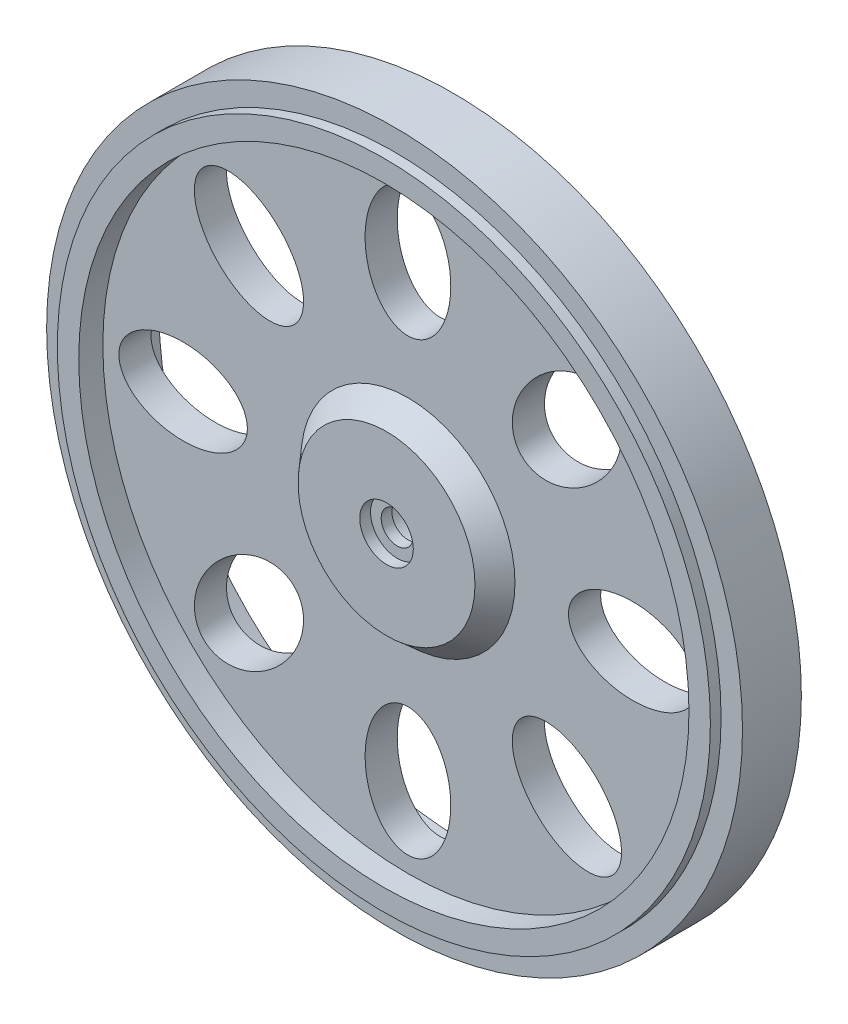
SolidWorks part; units mm, degrees
ref_plane "Front Plane" through (0, 0, 0) normal (0, 0, 1) x (1, 0, 0)
ref_plane "Top Plane" through (0, 0, 0) normal (0, 1, 0) x (1, 0, 0)
ref_plane "Right Plane" through (0, 0, 0) normal (1, 0, 0) x (0, 0, -1)
sketch "Sketch1" plane through (0, 0, 0) normal (1, 0, 0) x (0, 0, -1)
  line L0 (-21.1884, 0) -> (23.9372, 0) construction
  line L1 (0, -14.3976) -> (0, 60.2728) construction
  line L2 (-3.75, 28.5) -> (-1.5, 28.5)
  line L3 (-3.75, 28.5) -> (-3.75, 30.5)
  line L4 (-3.75, 30.5) -> (-2.75, 30.5)
  line L5 (-2.75, 30.5) -> (-2.75, 32.5)
  line L6 (-2.75, 32.5) -> (2.75, 32.5)
  line L7 (3.75, 30.5) -> (2.75, 30.5)
  line L8 (3.75, 28.5) -> (3.75, 30.5)
  line L9 (2.75, 30.5) -> (2.75, 32.5)
  line L10 (-1.5, 28.5) -> (-1.5, 0)
  line L11 (1.5, 28.5) -> (1.5, 0)
  line L12 (1.5, 0) -> (-1.5, 0)
  line L14 (1.5, 28.5) -> (3.75, 28.5)
  point P15 (0, 32.5)
  dimension "D1" = 7.5
  dimension "D2" = 2
  dimension "D3" = 2
  dimension "D4" = 2.75
  dimension "D5" = 32.5
  dimension "D6" = 1.5
revolve "Revolve1" add sketch "Sketch1" angle 360 about L0
sketch "Sketch2" plane through (0, 0, 1.5) normal (0, 0, 1) x (1, 0, 0)
  circle A0 centre (0, 0) radius 10
  dimension "D1" = 20
extrude "Extrude1" add sketch "Sketch2" along normal blind 2 draft 41
sketch "Sketch3" plane through (0, 0, -1.5) normal (0, 0, -1) x (-1, 0, 0)
  circle A0 centre (0, 0) radius 5.5
  dimension "D1" = 11
extrude "Extrude2" add sketch "Sketch3" along normal blind 4 draft 15
sketch "Sketch4" plane through (0, 0, 3.5) normal (0, 0, 1) x (1, 0, 0)
  circle A0 centre (0, 0) radius 2.5
  dimension "D1" = 5
extrude "Extrude3" cut sketch "Sketch4" against normal blind 1
sketch "Sketch5" plane through (0, 0, 2.5) normal (0, 0, 1) x (1, 0, 0)
  circle A0 centre (0, 0) radius 1.5
  dimension "D1" = 3
extrude "Extrude4" cut sketch "Sketch5" against normal blind 15 and the other way blind 24
sketch "Sketch6" plane through (0, 0, 1.5) normal (0, 0, 1) x (1, 0, 0)
  ellipse E0 centre (0, 21) end of major axis (0, 27) minor radius 4
  dimension "D1" = 8
  dimension "D2" = 12
  dimension "D3" = 15
extrude "Extrude5" cut sketch "Sketch6" against normal blind 15
pattern_circular "CirPattern2" count 8 over 360 about axis through (0, 0, 21.1884) along (0, 0, 1) of "Extrude5"
sketch "Sketch7" plane through (0, 0, -5.5) normal (0, 0, -1) x (-1, 0, 0)
  circle A0 centre (0, 0) radius 2.75
  dimension "D1" = 5.5
extrude "Extrude6" cut sketch "Sketch7" against normal blind 7
